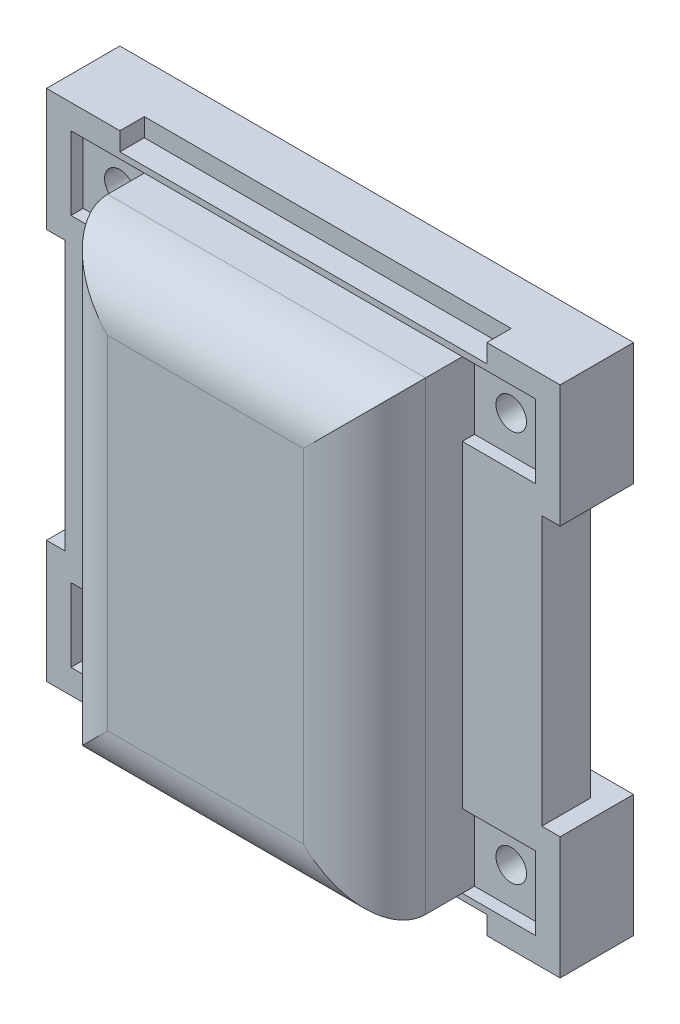
SolidWorks part; units mm, degrees
ref_plane "正面" through (0, 0, 0) normal (0, 0, 1) x (1, 0, 0)
ref_plane "平面" through (0, 0, 0) normal (0, 1, 0) x (1, 0, 0)
ref_plane "右側面" through (0, 0, 0) normal (1, 0, 0) x (0, 0, -1)
sketch "ｽｹｯﾁ1" plane through (0, 0, 0) normal (0, 0, 1) x (1, 0, 0)
  line L1 (13, -19) -> (-13, -19)
  line L2 (13, -19) -> (13, 19)
  line L3 (13, 19) -> (-13, 19)
  line L4 (-13, -19) -> (-13, 19)
  line L5 (13, -19) -> (-13, 19) construction
  line L6 (13, 19) -> (-13, -19) construction
  point P0 (0, 0)
  dimension "D1" = 38
  dimension "D2" = 26
extrude "ﾎﾞｽ - 押し出し1" add sketch "ｽｹｯﾁ1" along normal blind 12
sketch "ｽｹｯﾁ2" plane through (0, 0, 0) normal (0, 0, 1) x (1, 0, 0)
  line L1 (11, -17) -> (-11, -17)
  line L2 (11, -17) -> (11, 17)
  line L3 (11, 17) -> (-11, 17)
  line L4 (-11, -17) -> (-11, 17)
  line L5 (11, -17) -> (-11, 17) construction
  line L6 (11, 17) -> (-11, -17) construction
  point P0 (0, 0)
  dimension "D1" = 22
  dimension "D2" = 34
extrude "ｶｯﾄ - 押し出し1" cut sketch "ｽｹｯﾁ2" along normal blind 10
sketch "ｽｹｯﾁ3" plane through (0, 0, 0) normal (0, 0, 1) x (1, 0, 0)
  line L0 (13, 19) -> (-13, 19) construction
  line L1 (-0.8522, 2) -> (1.1478, 2)
  line L2 (-0.8522, 2) -> (-0.8522, 9)
  line L3 (-0.8522, 9) -> (1.1478, 9)
  line L4 (1.1478, 2) -> (1.1478, 9)
  line L5 (-0.8522, 2) -> (1.1478, 9) construction
  line L6 (-0.8522, 9) -> (1.1478, 2) construction
  point P0 (0.1478, 5.5)
  dimension "D1" = 7
  dimension "D2" = 2
  dimension "D3" = 10
sketch "ｽｹｯﾁ4" plane through (0, 0, 0) normal (0, 0, 1) x (1, 0, 0)
  line L0 (13, -19) -> (13, 19) construction
  line L1 (13, 19) -> (19, 19)
  line L2 (13, 19) -> (13, 13)
  line L3 (13, 13) -> (19, 13)
  line L4 (19, 19) -> (19, 13)
  line L5 (13, -19) -> (19, -19)
  line L6 (13, -19) -> (13, -13)
  line L7 (13, -13) -> (19, -13)
  line L8 (19, -19) -> (19, -13)
  line L9 (-13, -19) -> (13, -19) construction
  line L10 (-13, -19) -> (-19, -19)
  line L11 (-13, -19) -> (-13, -13)
  line L12 (-13, -13) -> (-19, -13)
  line L13 (-19, -19) -> (-19, -13)
  line L14 (-13, 19) -> (-19, 19)
  line L15 (-13, 19) -> (-13, 13)
  line L16 (-13, 13) -> (-19, 13)
  line L17 (-19, 19) -> (-19, 13)
  dimension "D1" = 6
  dimension "D2" = 6
  dimension "D3" = 6
  dimension "D4" = 6
  dimension "D5" = 6
  dimension "D6" = 6
  dimension "D7" = 6
  dimension "D8" = 6
  dimension "D9" = 0
extrude "ﾎﾞｽ - 押し出し2" add sketch "ｽｹｯﾁ4" along normal blind 3
fillet "ﾌｨﾚｯﾄ1" radius 5 4 edges at (0, 19, 12) (0, -19, 12) (13, 0, 12) (-13, 0, 12)
sketch "ｽｹｯﾁ6" plane through (0, 0, 0) normal (0, 0, -1) x (-1, 0, 0)
  line L1 (-15, -21) -> (15, -21)
  line L2 (-15, -21) -> (-15, 21)
  line L3 (-15, 21) -> (15, 21)
  line L4 (15, -21) -> (15, 21)
  line L5 (-15, -21) -> (15, 21) construction
  line L6 (-15, 21) -> (15, -21) construction
  line L7 (-13.5, -19.5) -> (13.5, -19.5)
  line L8 (-13.5, -19.5) -> (-13.5, 19.5)
  line L9 (-13.5, 19.5) -> (13.5, 19.5)
  line L10 (13.5, -19.5) -> (13.5, 19.5)
  line L11 (-13.5, -19.5) -> (13.5, 19.5) construction
  line L12 (-13.5, 19.5) -> (13.5, -19.5) construction
  point P0 (0, 0)
  point P6 (0, 0)
  dimension "D1" = 42
  dimension "D2" = 30
  dimension "D3" = 39
  dimension "D4" = 27
extrude "ﾎﾞｽ - 押し出し3" add sketch "ｽｹｯﾁ6" along normal blind 2 and the other way blind 2
sketch "ｽｹｯﾁ5" plane through (0, 0, 0) normal (0, 0, 1) x (1, 0, 0)
  line L0 (-13, 19) -> (-19, 19) construction
  line L1 (-19, 19) -> (-19, 13) construction
  line L2 (-13, -13) -> (-19, -13) construction
  line L3 (19, -19) -> (19, -13) construction
  line L4 (-19, -13) -> (-19, -19) construction
  line L5 (19, -13) -> (13, -13) construction
  line L6 (19, 13) -> (19, 19) construction
  line L7 (19, 19) -> (13, 19) construction
  circle A0 centre (-16, 16) radius 1.25
  circle A1 centre (-16, -16) radius 1.25
  circle A2 centre (16, -16) radius 1.25
  circle A3 centre (16, 16) radius 1.25
  dimension "D1" = 3
  dimension "D2" = 3
  dimension "D3" = 3
  dimension "D4" = 2.5
  dimension "D5" = 2.5
  dimension "D6" = 3
  dimension "D7" = 2.5
  dimension "D8" = 2.5
  dimension "D9" = 3
  dimension "D10" = 3
  dimension "D11" = 3
  dimension "D12" = 3
extrude "ｶｯﾄ - 押し出し4" cut sketch "ｽｹｯﾁ5" along normal through all and the other way through all
sketch "ｽｹｯﾁ10" plane through (0, 0, 2) normal (0, 0, 1) x (1, 0, 0)
  line L1 (-20, -20) -> (20, -20)
  line L2 (-20, -20) -> (-20, 20)
  line L3 (-20, 20) -> (20, 20)
  line L4 (20, -20) -> (20, 20)
  line L5 (-20, -20) -> (20, 20) construction
  line L6 (-20, 20) -> (20, -20) construction
  point P0 (0, 0)
  dimension "D1" = 40
  dimension "D2" = 40
sketch "ｽｹｯﾁ7" plane through (0, 0, 3) normal (0, 0, -1) x (-1, 0, 0)
  line L0 (-13, 13) -> (-13, -13) construction
  line L5 (13, 13) -> (19, 19) construction
  line L6 (13, 19) -> (19, 13) construction
  line L11 (13, -19) -> (19, -13) construction
  line L12 (13, -13) -> (19, -19) construction
  line L17 (-19, -19) -> (-13, -13) construction
  line L18 (-19, -13) -> (-13, -19) construction
  line L19 (-15, -13) -> (-13.5, -13) construction
  line L20 (-13, 19) -> (-8, 14) construction
  line L25 (-19, 13) -> (-13, 19) construction
  line L26 (-19, 19) -> (-13, 13) construction
  line L27 (-13, 19) -> (-13, 13) construction
  line L29 (-12.5, 12.5) -> (-19.5, 12.5)
  line L30 (-12.5, 12.5) -> (-12.5, 19.5)
  line L31 (-12.5, 19.5) -> (-19.5, 19.5)
  line L32 (-19.5, 12.5) -> (-19.5, 19.5)
  line L33 (-12.5, 12.5) -> (-19.5, 19.5) construction
  line L34 (-12.5, 19.5) -> (-19.5, 12.5) construction
  line L35 (19.5, 12.5) -> (12.5, 12.5)
  line L36 (19.5, 12.5) -> (19.5, 19.5)
  line L37 (19.5, 19.5) -> (12.5, 19.5)
  line L38 (12.5, 12.5) -> (12.5, 19.5)
  line L39 (19.5, 12.5) -> (12.5, 19.5) construction
  line L40 (19.5, 19.5) -> (12.5, 12.5) construction
  line L41 (19.5, -19.5) -> (12.5, -19.5)
  line L42 (19.5, -19.5) -> (19.5, -12.5)
  line L43 (19.5, -12.5) -> (12.5, -12.5)
  line L44 (12.5, -19.5) -> (12.5, -12.5)
  line L45 (19.5, -19.5) -> (12.5, -12.5) construction
  line L46 (19.5, -12.5) -> (12.5, -19.5) construction
  line L47 (-12.5, -19.5) -> (-19.5, -19.5)
  line L48 (-12.5, -19.5) -> (-12.5, -12.5)
  line L49 (-12.5, -12.5) -> (-19.5, -12.5)
  line L50 (-19.5, -19.5) -> (-19.5, -12.5)
  line L51 (-12.5, -19.5) -> (-19.5, -12.5) construction
  line L52 (-12.5, -12.5) -> (-19.5, -19.5) construction
  point P0 (16, 16)
  point P7 (16, -16)
  point P14 (-16, -16)
  point P24 (-16, 16)
  point P34 (-16, 16)
  point P39 (16, 16)
  point P44 (16, -16)
  point P49 (-16, -16)
  dimension "D1" = 7
  dimension "D2" = 7
  dimension "D3" = 7
  dimension "D4" = 7
  dimension "D5" = 7
  dimension "D6" = 7
  dimension "D7" = 7
  dimension "D8" = 7
extrude "ｶｯﾄ - 押し出し5" cut sketch "ｽｹｯﾁ7" against normal blind 2 from offset 5
sketch "ｽｹｯﾁ8" plane through (0, 0, 0) normal (0, 0, 1) x (1, 0, 0)
  line L0 (15, 21) -> (15, 19.5)
  line L1 (15, 11) -> (21, 11)
  line L2 (-15, 21) -> (-15, 19.5)
  line L3 (15, 21) -> (21, 21)
  line L4 (21, 11) -> (21, 21)
  line L5 (11, 11) -> (21, 21) construction
  line L6 (11, 21) -> (21, 11) construction
  line L7 (-15, 19.5) -> (-19.5, 19.5)
  line L8 (-19.5, 19.5) -> (-19.5, 12.5)
  line L9 (-19.5, 12.5) -> (-15, 12.5)
  line L10 (15, 12.5) -> (15, 11)
  line L12 (15, -21) -> (21, -21)
  line L14 (15, -11) -> (21, -11)
  line L15 (21, -21) -> (21, -11)
  line L16 (11, -21) -> (21, -11) construction
  line L17 (11, -11) -> (21, -21) construction
  line L18 (-21, -21) -> (-15, -21)
  line L19 (-21, -21) -> (-21, -11)
  line L20 (-21, -11) -> (-15, -11)
  line L21 (15, 19.5) -> (19.5, 19.5)
  line L22 (-21, -21) -> (-11, -11) construction
  line L23 (-21, -11) -> (-11, -21) construction
  line L24 (-21, 11) -> (-15, 11)
  line L25 (-21, 11) -> (-21, 21)
  line L26 (-21, 21) -> (-15, 21)
  line L27 (-15, -11) -> (-15, -12.5)
  line L28 (-21, 11) -> (-11, 21) construction
  line L29 (-21, 21) -> (-11, 11) construction
  line L30 (15, -11) -> (15, -12.5)
  line L34 (15, -19.5) -> (15, -21)
  line L37 (-15, 12.5) -> (-15, 11)
  line L42 (-15, -19.5) -> (-15, -21)
  line L43 (-15, -21) -> (-15, -19.5) construction
  line L44 (19.5, 19.5) -> (19.5, 12.5)
  line L45 (19.5, 12.5) -> (15, 12.5)
  line L46 (15, -12.5) -> (19.5, -12.5)
  line L47 (19.5, -12.5) -> (19.5, -19.5)
  line L48 (19.5, -19.5) -> (15, -19.5)
  line L49 (-15, -12.5) -> (-19.5, -12.5)
  line L50 (-19.5, -12.5) -> (-19.5, -19.5)
  line L51 (-19.5, -19.5) -> (-15, -19.5)
  point P0 (16, 16)
  point P16 (16, -16)
  point P25 (-16, -16)
  point P31 (-16, 16)
  dimension "D1" = 10
  dimension "D2" = 10
  dimension "D3" = 10
  dimension "D4" = 10
  dimension "D5" = 10
  dimension "D6" = 10
  dimension "D7" = 10
  dimension "D8" = 10
extrude "ﾎﾞｽ - 押し出し4" add sketch "ｽｹｯﾁ8" along normal blind 4 and the other way blind 2
sketch "ｽｹｯﾁ9" plane through (0, 0, 0) normal (0, 0, -1) x (-1, 0, 0)
  line L1 (-9, -15) -> (9, -15)
  line L2 (-9, -15) -> (-9, 15)
  line L3 (-9, 15) -> (9, 15)
  line L4 (9, -15) -> (9, 15)
  line L5 (-9, -15) -> (9, 15) construction
  line L6 (-9, 15) -> (9, -15) construction
  line L7 (-10.5, -16.5) -> (10.5, -16.5)
  line L8 (-10.5, -16.5) -> (-10.5, 16.5)
  line L9 (-10.5, 16.5) -> (10.5, 16.5)
  line L10 (10.5, -16.5) -> (10.5, 16.5)
  line L11 (-10.5, -16.5) -> (10.5, 16.5) construction
  line L12 (-10.5, 16.5) -> (10.5, -16.5) construction
  point P0 (0, 0)
  point P6 (0, 0)
  dimension "D1" = 30
  dimension "D2" = 18
  dimension "D3" = 21
  dimension "D4" = 33
extrude "ﾎﾞｽ - 押し出し5" add sketch "ｽｹｯﾁ9" along normal blind 2 and the other way blind 8
sketch "ｽｹｯﾁ11" plane through (0, 0, 2) normal (0, 0, 1) x (1, 0, 0)
  line L0 (-19, 13) -> (-13, 13)
  line L1 (19.5, -19.5) -> (-19.5, -19.5)
  line L2 (19.5, -19.5) -> (19.5, 19.5)
  line L3 (19.5, 19.5) -> (-19.5, 19.5)
  line L4 (-19.5, -19.5) -> (-19.5, 19.5)
  line L5 (19.5, -19.5) -> (-19.5, 19.5) construction
  line L6 (19.5, 19.5) -> (-19.5, -19.5) construction
  line L7 (19, -19) -> (-19, -19)
  line L8 (19, -19) -> (19, -13)
  line L9 (19, 19) -> (-19, 19)
  line L10 (-19, -19) -> (-19, -13)
  line L11 (19, -19) -> (-19, 19) construction
  line L12 (19, 19) -> (-19, -19) construction
  line L13 (-13, 13) -> (-13, -13)
  line L14 (-13, -13) -> (-19, -13)
  line L15 (-19, 13) -> (-19, 19)
  line L16 (19, 13) -> (13, 13)
  line L17 (13, 13) -> (13, -13)
  line L18 (13, 19) -> (13, -19) construction
  line L19 (13, -13) -> (19, -13)
  line L20 (19, 13) -> (19, 19)
  point P0 (0, 0)
  point P7 (0, 0)
extrude "ﾎﾞｽ - 押し出し9" add sketch "ｽｹｯﾁ11" along normal blind 2 and the other way blind 2
